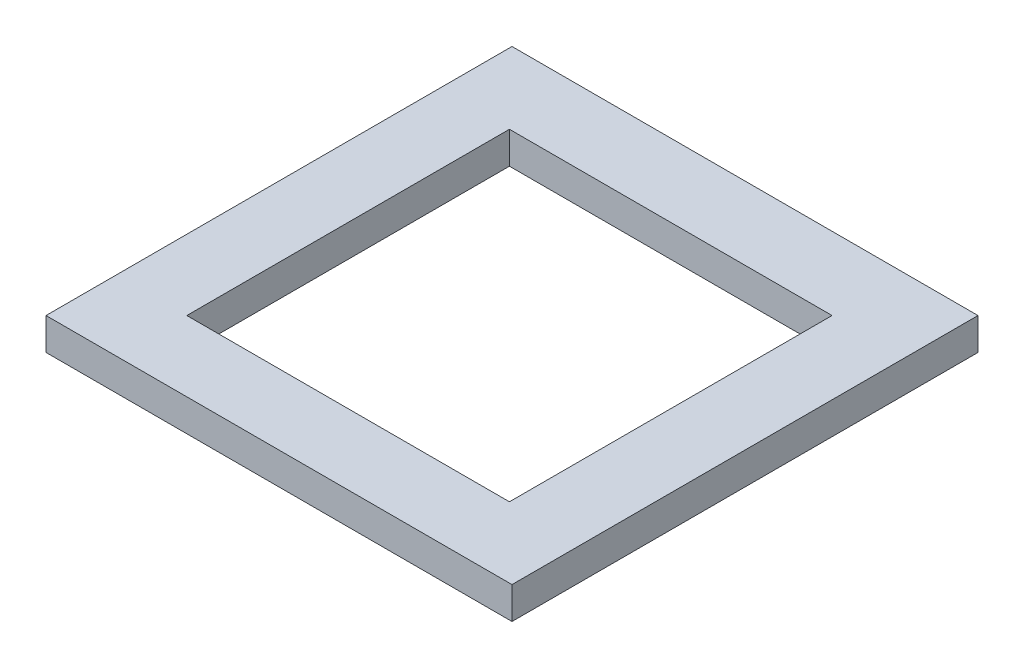
SolidWorks part; units mm, degrees
ref_plane "Front Plane" through (0, 0, 0) normal (0, 0, 1) x (1, 0, 0)
ref_plane "Top Plane" through (0, 0, 0) normal (0, 1, 0) x (1, 0, 0)
ref_plane "Right Plane" through (0, 0, 0) normal (1, 0, 0) x (0, 0, -1)
sketch "Sketch1" plane through (0, 0, 0) normal (0, 1, 0) x (1, 0, 0)
  line L1 (250.2475, 285.2878) -> (296.4755, 285.2878)
  line L2 (250.2475, 285.2878) -> (250.2475, 331.5158)
  line L3 (250.2475, 331.5158) -> (296.4755, 331.5158)
  line L4 (296.4755, 285.2878) -> (296.4755, 331.5158)
  line L7 (257.2325, 292.2728) -> (289.2365, 292.2728)
  line L8 (257.2325, 292.2728) -> (257.2325, 324.2768)
  line L9 (257.2325, 324.2768) -> (289.2365, 324.2768)
  line L10 (289.2365, 292.2728) -> (289.2365, 324.2768)
  circle A0 centre (255.7933, 292.6953) radius 1.5 construction
  point P0 (0, 0)
  point P6 (0, 0)
  dimension "D1" = 46.228
  dimension "D2" = 46.228
  dimension "D3" = 32.004
  dimension "D4" = 7.239
  dimension "D5" = 7.239
extrude "Boss-Extrude1" add sketch "Sketch1" along normal blind 3.175
